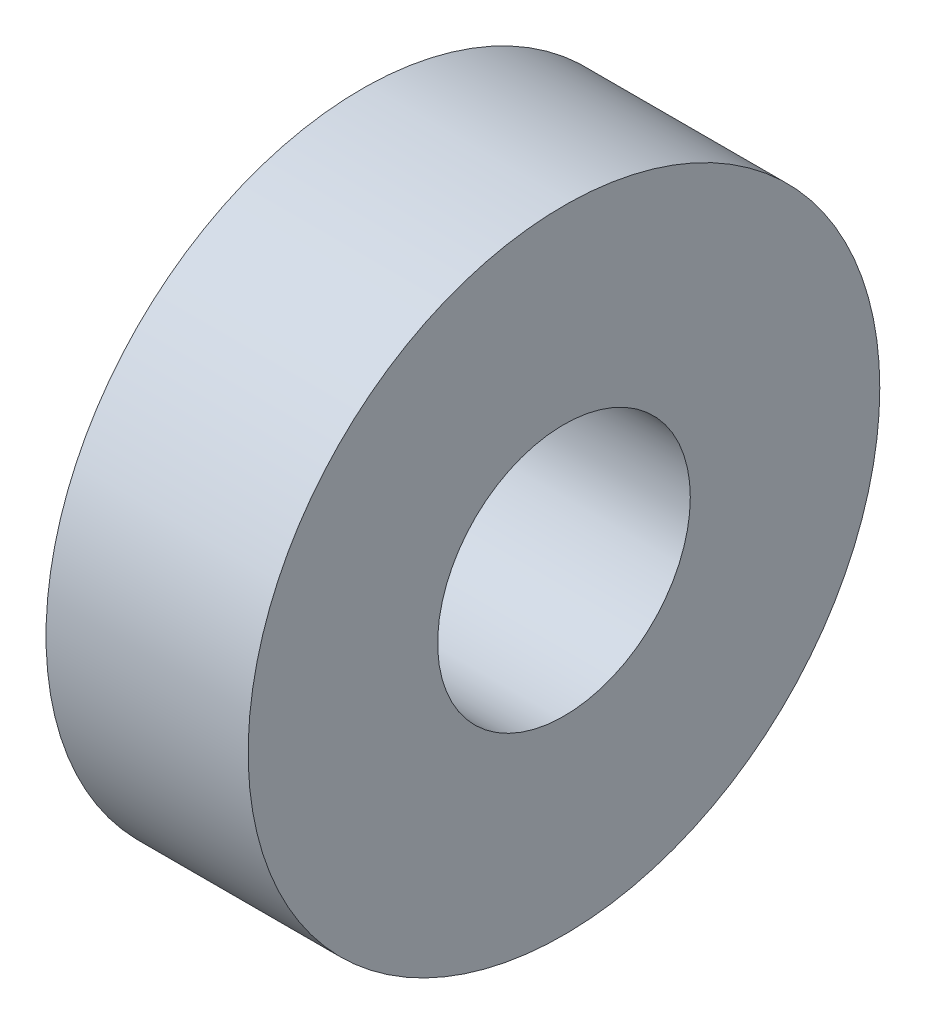
SolidWorks part; units mm, degrees
ref_plane "Front Plane" through (0, 0, 0) normal (0, 0, 1) x (1, 0, 0)
ref_plane "Top Plane" through (0, 0, 0) normal (0, 1, 0) x (1, 0, 0)
ref_plane "Right Plane" through (0, 0, 0) normal (1, 0, 0) x (0, 0, -1)
sketch "Sketch1" plane through (0, 0, 0) normal (1, 0, 0) x (0, 0, -1)
  circle A0 centre (0, 0) radius 3.175
  circle A1 centre (0, 0) radius 7.9375
  dimension "D1" = 6.35
  dimension "D2" = 15.875
extrude "Boss-Extrude1" add sketch "Sketch1" along normal blind 5.08
